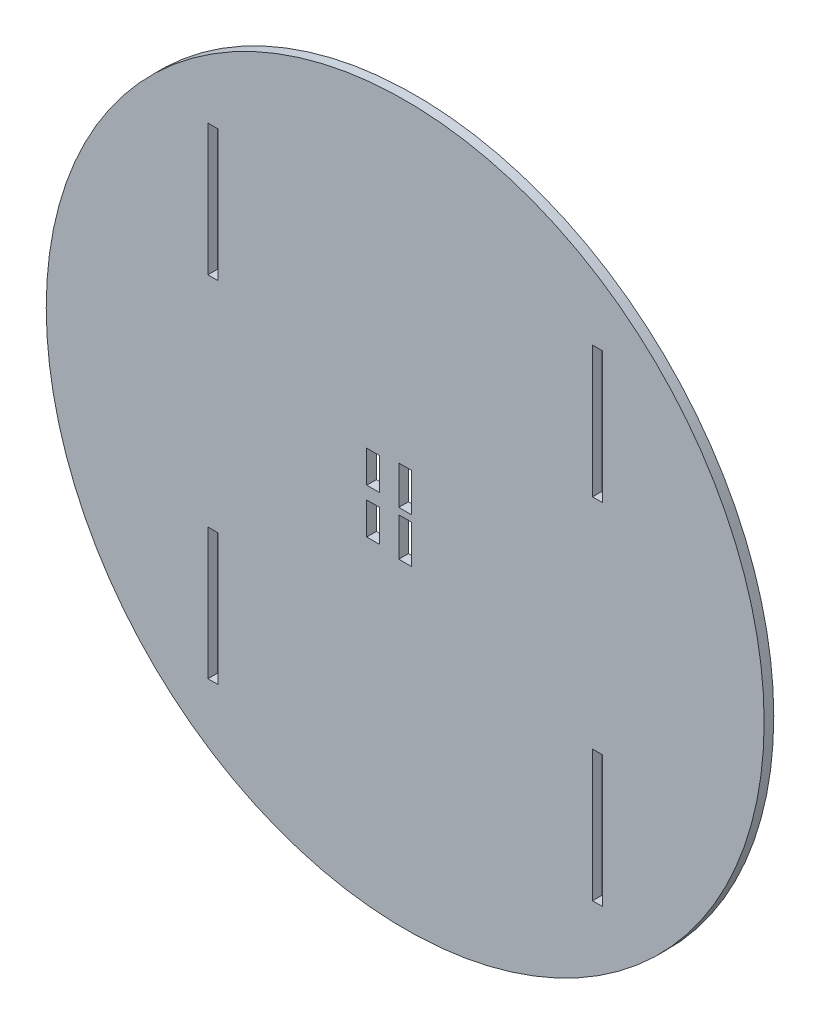
SolidWorks part; units mm, degrees
ref_plane "Front Plane" through (0, 0, 0) normal (0, 0, 1) x (1, 0, 0)
ref_plane "Top Plane" through (0, 0, 0) normal (0, 1, 0) x (1, 0, 0)
ref_plane "Right Plane" through (0, 0, 0) normal (1, 0, 0) x (0, 0, -1)
sketch "Sketch1" plane through (0, 0, 0) normal (0, 0, 1) x (1, 0, 0)
  line L0 (-60, 96.516) -> (-60, -96.516) construction
  line L1 (60, 113.1241) -> (60, -109.3006) construction
  line L3 (-61.55, 75.0727) -> (-58.45, 75.0727)
  line L4 (-61.55, 75.0727) -> (-61.55, 34.0727)
  line L5 (-61.55, 34.0727) -> (-58.45, 34.0727)
  line L6 (-58.45, 75.0727) -> (-58.45, 34.0727)
  line L7 (-61.55, 75.0727) -> (-58.45, 34.0727) construction
  line L8 (-61.55, 34.0727) -> (-58.45, 75.0727) construction
  line L9 (-61.55, -34.0727) -> (-58.45, -34.0727)
  line L10 (-61.55, -34.0727) -> (-61.55, -75.0727)
  line L11 (-61.55, -75.0727) -> (-58.45, -75.0727)
  line L12 (-58.45, -34.0727) -> (-58.45, -75.0727)
  line L13 (-61.55, -34.0727) -> (-58.45, -75.0727) construction
  line L14 (-61.55, -75.0727) -> (-58.45, -34.0727) construction
  line L15 (58.45, 75.0727) -> (61.55, 75.0727)
  line L16 (58.45, 75.0727) -> (58.45, 34.0727)
  line L17 (58.45, 34.0727) -> (61.55, 34.0727)
  line L18 (61.55, 75.0727) -> (61.55, 34.0727)
  line L19 (58.45, 75.0727) -> (61.55, 34.0727) construction
  line L20 (58.45, 34.0727) -> (61.55, 75.0727) construction
  line L21 (58.45, -34.0727) -> (61.55, -34.0727)
  line L22 (58.45, -34.0727) -> (58.45, -75.0727)
  line L23 (58.45, -75.0727) -> (61.55, -75.0727)
  line L24 (61.55, -34.0727) -> (61.55, -75.0727)
  line L25 (58.45, -34.0727) -> (61.55, -75.0727) construction
  line L26 (58.45, -75.0727) -> (61.55, -34.0727) construction
  line L27 (-2, 13) -> (2, 13)
  line L28 (-2, 13) -> (-2, 1)
  line L29 (-2, 1) -> (2, 1)
  line L30 (2, 13) -> (2, 1)
  line L31 (-2, 13) -> (2, 1) construction
  line L32 (-2, 1) -> (2, 13) construction
  line L33 (-2, -1) -> (2, -1)
  line L34 (-2, -1) -> (-2, -13)
  line L35 (-2, -13) -> (2, -13)
  line L36 (2, -1) -> (2, -13)
  line L37 (-2, -1) -> (2, -13) construction
  line L38 (-2, -13) -> (2, -1) construction
  line L39 (-12, 12) -> (-8, 12)
  line L40 (-12, 12) -> (-12, 2)
  line L41 (-12, 2) -> (-8, 2)
  line L42 (-8, 12) -> (-8, 2)
  line L43 (-12, 12) -> (-8, 2) construction
  line L44 (-12, 2) -> (-8, 12) construction
  line L45 (-12, -2) -> (-8, -2)
  line L46 (-12, -2) -> (-12, -12)
  line L47 (-12, -12) -> (-8, -12)
  line L48 (-8, -2) -> (-8, -12)
  line L49 (-12, -2) -> (-8, -12) construction
  line L50 (-12, -12) -> (-8, -2) construction
  circle A0 centre (0, 0) radius 112
  point P6 (-60, 54.5727)
  point P12 (-60, -54.5727)
  point P17 (60, 54.5727)
  point P22 (60, -54.5727)
  point P27 (60, 94.5727)
  point P28 (60, -94.5727)
  point P29 (-60, -94.5727)
  point P30 (-60, 94.5727)
  point P31 (0, 7)
  point P36 (0, -7)
  point P41 (-10, 7)
  point P46 (-10, -7)
  dimension "D1" = 224
  dimension "D2" = 60
  dimension "D3" = 60
  dimension "D4" = 41
  dimension "D5" = 3.1
  dimension "D6" = 41
  dimension "D7" = 3.1
  dimension "D8" = 3.1
  dimension "D9" = 41
  dimension "D10" = 41
  dimension "D11" = 3.1
  dimension "D12" = 40
  dimension "D13" = 40
  dimension "D14" = 40
  dimension "D15" = 40
  dimension "D16" = 1
  dimension "D17" = 1
  dimension "D18" = 12
  dimension "D19" = 4
  dimension "D20" = 4
  dimension "D21" = 12
  dimension "D22" = 10
  dimension "D23" = 10
  dimension "D24" = 10
  dimension "D25" = 4
  dimension "D26" = 4
  dimension "D27" = 10
extrude "Boss-Extrude1" add sketch "Sketch1" along normal mid plane 3
ref_plane "Plane1" through (0, 0, 1.5) normal (0, 0, 1) x (1, 0, 0)
sketch "Sketch2" plane through (0, 0, 1.5) normal (0, 0, 1) x (1, 0, 0)
  point P0 (0, 0)
